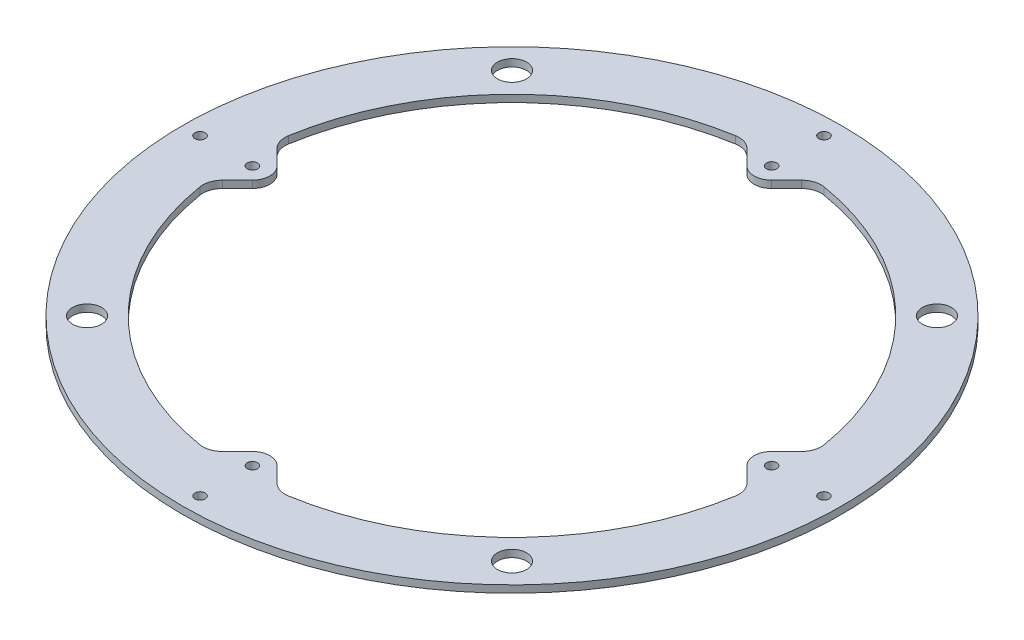
SolidWorks part; units mm, degrees
material "1023 Carbon Steel Sheet (SS)"
ref_plane "Front Plane" through (0, 0, 0) normal (0, 0, 1) x (1, 0, 0)
ref_plane "Top Plane" through (0, 0, 0) normal (0, 1, 0) x (1, 0, 0)
ref_plane "Right Plane" through (0, 0, 0) normal (1, 0, 0) x (0, 0, -1)
sketch "Sketch1" plane through (0, 0, 0) normal (0, 1, 0) x (1, 0, 0)
  circle A0 centre (0, 0) radius 177.8
  circle A1 centre (0, 0) radius 215.9
  dimension "D1" = 355.6
  dimension "D2" = 38.1
extrude "Boss-Extrude1" add sketch "Sketch1" along normal blind 4.7498
sketch "Sketch3" plane through (0, 0, 0) normal (0, 1, 0) x (1, 0, 0)
  line L0 (-22.4506, 176.3769) -> (0, 153.9263)
  line L1 (0, 153.9263) -> (22.4506, 176.3769)
  circle A0 centre (0, 0) radius 177.8 construction
  arc A1 (22.4506, 176.3769) -> (-22.4506, 176.3769) centre (0, 0) ccw
  dimension "D1" = 31.75
extrude "Boss-Extrude2" add sketch "Sketch3" along normal up to surface (4.7498 mm away) up to face at (0, 4.7498, 215.9)
fillet "Fillet2" radius 12.7 2 edges at (22.4506, 2.3749, -176.3769) (-22.4506, 2.3749, -176.3769)
fillet "Fillet3" radius 11.43 1 edges at (0, 2.3749, -153.9263)
sketch "Sketch4" plane through (0, 4.7498, 0) normal (0, 1, 0) x (1, 0, 0)
  circle A1 centre (0, 170.0907) radius 11.4992 construction
  point P0 (0, 170.0907)
  point P1 (0, 204.3807)
  dimension "D1" = 34.29
hole_wizard "1/4 Clearance Hole1" positions "Sketch4" profile "Sketch5" hole size "1/4" standard "ANSI Inch"
sketch "Sketch5" plane through (0, 4.7498, -170.0907) normal (1, 0, 0) x (0, 0, 1)
  line L0 (0, 0) -> (0, 12.1898)
  line L1 (0, 12.1898) -> (3.3782, 10.16)
  line L2 (3.3782, 10.16) -> (3.3782, 0)
  line L5 (3.3782, 0) -> (0, 0)
  line L10 (0, 12.1898) -> (-3.3782, 10.16) construction
  line L11 (0, -6.35) -> (0, 107.95) construction
  dimension "Hole Dia." = 6.7564
  dimension "Hole Depth" = 10.16
  dimension "Drill Angle" = 118
pattern_circular "CirPattern1" count 4 over 360 about axis through (0, 0, 0) along (0, 1, 0) of "Boss-Extrude2", "Fillet2", "Fillet3", "1/4 Clearance Hole1"
sketch "Sketch6" plane through (0, 4.7498, 0) normal (0, 1, 0) x (1, 0, 0)
  line L0 (0, 0) -> (-215.9, 0) construction
  line L1 (0, 0) -> (-139.194, 139.194) construction
  line L2 (-125.7236, 125.7236) -> (-152.6644, 152.6644) construction
  circle A0 centre (-139.194, 139.194) radius 9.525
  circle A1 centre (0, 0) radius 215.9 construction
  arc A3 (-28.9952, 175.4198) -> (-175.4198, 28.9952) centre (0, 0) ccw construction
  point P8 (-139.194, 139.194)
  dimension "D2" = 19.05
  dimension "D1" = 45
extrude "Cut-Extrude1" cut sketch "Sketch6" against normal up to next (4.7498 mm away)
pattern_circular "CirPattern2" count 4 over 360 about axis through (0, 0, 0) along (0, 1, 0) of "Cut-Extrude1"
